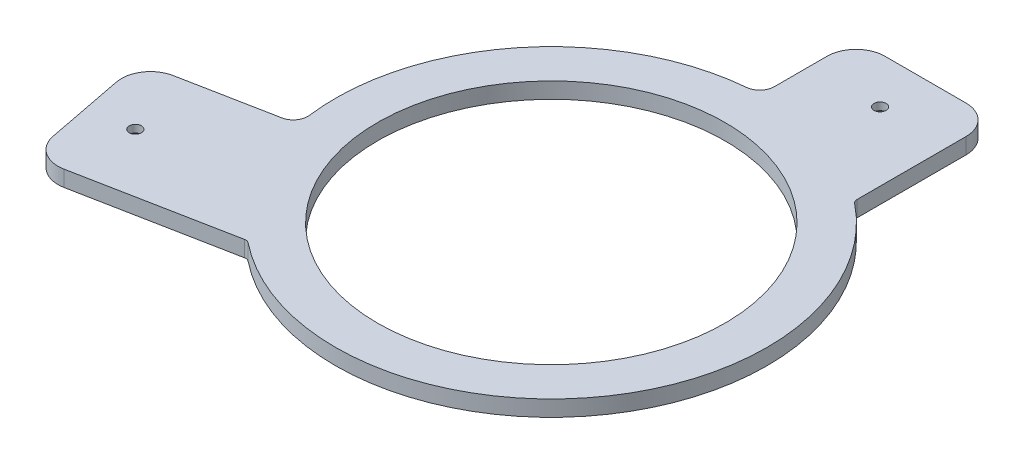
SolidWorks part; units mm, degrees
ref_plane "Front Plane" through (0, 0, 0) normal (0, 0, 1) x (1, 0, 0)
ref_plane "Top Plane" through (0, 0, 0) normal (0, 1, 0) x (1, 0, 0)
ref_plane "Right Plane" through (0, 0, 0) normal (1, 0, 0) x (0, 0, -1)
sketch "Sketch1" plane through (0, 0, 0) normal (0, 1, 0) x (1, 0, 0)
  line L0 (0, 127.6607) -> (0, -89.2536) construction
  line L1 (118.0509, 0) -> (-117.6932, 0) construction
  line L2 (0, 0) -> (-165.0874, -32.0897) construction
  line L3 (-119.0714, -23.1451) -> (-73.1312, -14.2153)
  line L4 (-109.9698, -69.9687) -> (-47.0743, -57.7431)
  line L5 (-119.0714, -23.1451) -> (-109.9698, -69.9687)
  line L6 (0, 0) -> (19.7722, -101.7192) construction
  line L7 (-2.2, 116.4776) -> (-2.2, 50.5289) construction
  line L8 (-2.2, 107.4) -> (45.8, 107.4)
  line L9 (-2.2, 107.4) -> (-2.2, 74.4675)
  line L10 (45.8, 107.4) -> (45.8, 58.7589)
  arc A0 (-47.0743, -57.7431) -> (45.8, 58.7589) centre (0, 0) ccw
  circle A1 centre (0, 0) radius 60
  arc A2 (-2.2, 74.4675) -> (-73.1312, -14.2153) centre (0, 0) ccw
  point P16 (-165.0874, -32.0897)
  dimension "D1" = 149
  dimension "D2" = 120
  dimension "D3" = 101
  dimension "D4" = 47.7
  dimension "D6" = 121.3
  dimension "D7" = 2.2
  dimension "D8" = 107.4
  dimension "D9" = 48
extrude "Boss-Extrude1" add sketch "Sketch1" along normal blind 5.5
fillet "Fillet1" radius 2 1 edges at (-47.0743, 2.75, 57.7431)
fillet "Fillet2" radius 10 4 edges at (45.8, 2.75, -107.4) (-2.2, 2.75, -107.4) (-119.0714, 2.75, 23.1451) (-109.9698, 2.75, 69.9687)
fillet "Fillet3" radius 5 2 edges at (-73.1312, 2.75, 14.2153) (-2.2, 2.75, -74.4675)
fillet "Fillet4" radius 2.15 1 edges at (45.8, 2.75, -58.7589)
hole_wizard "CSK for M4 SFHCS1" positions "Sketch2" profile "Sketch3" countersink size "M4" standard "ANSI Metric" end condition through all
sketch "Sketch2" plane through (0, 0, 0) normal (0, -1, 0) x (-1, 0, 0)
  line L0 (-35.8, 107.4) -> (-7.8, 107.4) construction
  line L1 (117.1633, -32.9614) -> (111.8779, -60.1525) construction
  line L2 (77.8849, -15.1393) -> (109.2551, -21.237) construction
  line L3 (2.2, 97.4) -> (2.2, 79.1733) construction
  point P0 (-22.1, 91.4)
  point P2 (99.7676, -43.842)
  dimension "D1" = 16
  dimension "D2" = 15
  dimension "D3" = 24
  dimension "D4" = 24.3
sketch "Sketch3" plane through (22.1, 0, -91.4) normal (1, 0, 0) x (0, 0, -1)
  line L0 (0, 0) -> (0, 5.5)
  line L1 (0, 5.5) -> (2.1, 5.5)
  line L2 (2.1, 5.5) -> (2.1, 2.9)
  line L3 (2.1, 2.9) -> (5, 0)
  line L5 (5, 0) -> (0, 0)
  line L6 (-2.1, 2.9) -> (-5, 0) construction
  line L11 (0, -6.35) -> (0, 107.95) construction
  dimension "Thru Hole Dia." = 4.2
  dimension "Thru Hole Depth" = 5.5
  dimension "Near C'Sink Dia." = 10
  dimension "Near C'Sink Angle" = 90
